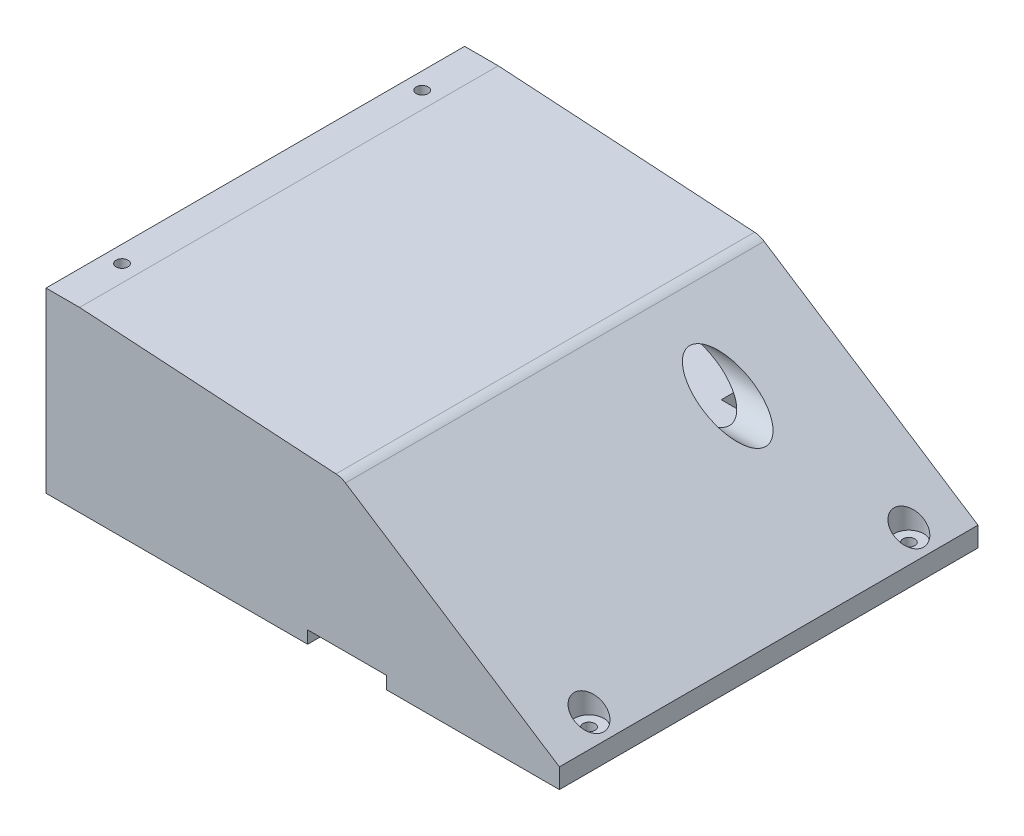
SolidWorks part; units mm, degrees
material "PE High Density"
ref_plane "Front Plane" through (0, 0, 0) normal (0, 0, 1) x (1, 0, 0)
ref_plane "Top Plane" through (0, 0, 0) normal (0, 1, 0) x (1, 0, 0)
ref_plane "Right Plane" through (0, 0, 0) normal (1, 0, 0) x (0, 0, -1)
sketch "Sketch1" plane through (0, 0, 0) normal (0, 0, 1) x (1, 0, 0)
  line L0 (0, 0) -> (-20, 0)
  line L3 (-242.9846, 20) -> (-242.9846, 25)
  line L4 (-242.9846, 25) -> (-260, 25)
  line L5 (-260, 25) -> (-260, 30)
  line L10 (-242.9846, 85) -> (-260, 85)
  line L11 (-260, 85) -> (-260, 90)
  line L14 (-242.9846, 90) -> (-260, 90)
  line L23 (-49.1581, 30) -> (-260, 30)
  line L26 (-49.1581, 30) -> (-122.3017, 77.5)
  line L27 (-260, 30) -> (-120, 30) construction
  line L28 (-260, 30) -> (-260, 67) construction
  line L29 (-260, 67) -> (-120, 67) construction
  line L30 (-120, 30) -> (-120, 67) construction
  line L31 (-110.512, 81.7673) -> (0, 10)
  line L32 (-20, 0) -> (-20, 20)
  line L35 (0, 0) -> (0, 10)
  line L36 (-242.9846, 20) -> (-20, 20)
  line L37 (-242.9846, 85) -> (-122.3017, 77.5)
  line L38 (-242.9846, 90) -> (-110.512, 81.7673)
  dimension "D1" = 20
  dimension "D2" = 20
  dimension "D3" = 10
  dimension "D4" = 55
  dimension "D5" = 5
  dimension "D6" = 140
  dimension "D7" = 37
  dimension "D9" = 33
  dimension "D10" = 10
  dimension "D11" = 260
  dimension "D13" = 222.9846
extrude "Boss-Extrude1" add sketch "Sketch1" along normal blind 212
sketch "Sketch2" plane through (0, 0, 0) normal (0, 0, -1) x (-1, 0, 0)
  line L2 (0, 0) -> (260, 0)
  line L3 (260, 0) -> (260, 90)
  line L5 (110.512, 81.7673) -> (0, 10)
  line L6 (0, 10) -> (0, 0)
  line L7 (260, 90) -> (110.512, 81.7673)
extrude "Boss-Extrude2" add sketch "Sketch2" against normal blind 10
sketch "Sketch3" plane through (0, 0, 212) normal (0, 0, 1) x (1, 0, 0)
  line L1 (-110.512, 81.7673) -> (0, 10)
  line L2 (0, 10) -> (0, 0)
  line L3 (0, 0) -> (-260, 0)
  line L4 (-260, 0) -> (-260, 90)
  line L5 (-260, 90) -> (-110.512, 81.7673)
extrude "Boss-Extrude3" add sketch "Sketch3" against normal blind 10
sketch "Sketch4" plane through (0, 0, 0) normal (0, -1, 0) x (1, 0, 0)
  line L0 (0, 212) -> (0, 0) construction
  line L4 (-260, 212) -> (0, 212) construction
  line L5 (0, 106) -> (-20, 106) construction
  line L6 (-20, 202) -> (-20, 10) construction
  circle A0 centre (-10, 187) radius 3
  circle A1 centre (-10, 25) radius 3
  dimension "D1" = 6
  dimension "D2" = 10
  dimension "D3" = 25
extrude "Cut-Extrude1" cut sketch "Sketch4" against normal through all
ref_plane "Plane1" through (0, 10, 0) normal (0, -1, 0) x (-1, 0, 0)
sketch "Sketch6" plane through (0, 10, 0) normal (0, -1, 0) x (-1, 0, 0)
  line L0 (0, -106) -> (20, -106) construction
  line L1 (0, -212) -> (0, 0) construction
  line L2 (20, -202) -> (20, -10) construction
  circle A0 centre (10, -25) radius 7.5
  circle A1 centre (10, -187) radius 7.5
  dimension "D1" = 15
extrude "Cut-Extrude2" cut sketch "Sketch6" against normal through all
sketch "Sketch7" plane through (0, 20, 0) normal (0, -1, 0) x (1, 0, 0)
  line L0 (-242.9846, 106) -> (-102.9846, 106) construction
  line L1 (-242.9846, 202) -> (-242.9846, 10) construction
  line L2 (-242.9846, 166) -> (-102.9846, 166) construction
  line L3 (-242.9846, 166) -> (-242.9846, 46) construction
  line L4 (-242.9846, 46) -> (-102.9846, 46) construction
  line L5 (-102.9846, 166) -> (-102.9846, 46) construction
  line L7 (-20, 10) -> (-260, 10) construction
  line L8 (-260, 202) -> (-20, 202) construction
  line L9 (-97.0991, 166) -> (-87.0991, 166)
  line L10 (-97.0991, 166) -> (-97.0991, 46)
  line L11 (-97.0991, 46) -> (-87.0991, 46)
  line L12 (-87.0991, 166) -> (-87.0991, 46)
  line L13 (-100, 30) -> (-40, 30)
  line L14 (-100, 30) -> (-100, 15)
  line L15 (-100, 15) -> (-40, 15)
  line L16 (-40, 30) -> (-40, 15)
  line L17 (-20, 202) -> (-20, 10) construction
  circle A0 centre (-161.4846, 161) radius 1.5
  circle A1 centre (-225.6846, 161) radius 1.5
  circle A2 centre (-161.4846, 51) radius 1.5
  circle A3 centre (-225.6846, 51) radius 1.5
  circle A4 centre (-67.9846, 136) radius 12.5
  dimension "D4" = 3
  dimension "D6" = 3
  dimension "D9" = 25
  dimension "D1" = 120
  dimension "D2" = 140
  dimension "D3" = 36
  dimension "D5" = 58.5
  dimension "D7" = 122.7
  dimension "D8" = 5
  dimension "D10" = 30
  dimension "D11" = 35
  dimension "D12" = 10
  dimension "D13" = 120
  dimension "D14" = 15
  dimension "D15" = 60
  dimension "D16" = 5
  dimension "D17" = 20
extrude "Cut-Extrude3" cut sketch "Sketch7" against normal blind 12.5
ref_plane "Plane2" through (-110.512, 0, 0) normal (-1, 0, 0) x (0, 0, 1)
sketch "Sketch8" plane through (-110.512, 0, 0) normal (-1, 0, 0) x (0, 0, 1)
  line L0 (202, 30) -> (30, 30) construction
  circle A0 centre (54, 57.25) radius 12.5
  point P4 (116, 30)
  dimension "D3" = 25
  dimension "D1" = 27.25
  dimension "D2" = 62
extrude "Cut-Extrude4" cut sketch "Sketch8" against normal up to next
sketch "Sketch9" plane through (0, 25, 0) normal (0, -1, 0) x (1, 0, 0)
  line L0 (-242.9846, 202) -> (-260, 202) construction
  line L1 (-260, 202) -> (-260, 10) construction
  line L2 (-242.9846, 106) -> (-260, 106) construction
  line L3 (-242.9846, 202) -> (-242.9846, 10) construction
  circle A0 centre (-251.5, 182) radius 3
  circle A1 centre (-251.5, 30) radius 3
  dimension "D1" = 20
  dimension "D3" = 6
  dimension "D2" = 8.5
extrude "Cut-Extrude5" cut sketch "Sketch9" against normal through all both and the other way through all
sketch "Sketch10" plane through (0, 0, 212) normal (0, 0, 1) x (1, 0, 0)
  line L0 (-260, 0) -> (0, 0) construction
  line L1 (-127.5, 0) -> (-87.5, 0)
  line L2 (-127.5, 0) -> (-127.5, 6.35)
  line L3 (-127.5, 6.35) -> (-87.5, 6.35)
  line L4 (-87.5, 0) -> (-87.5, 6.35)
  line L5 (0, 0) -> (0, 10) construction
  dimension "D1" = 87.5
  dimension "D2" = 40
  dimension "D3" = 6.35
extrude "Cut-Extrude6" cut sketch "Sketch10" against normal through all both
fillet "Fillet1" radius 10 1 edges at (-110.512, 81.7673, 106)
